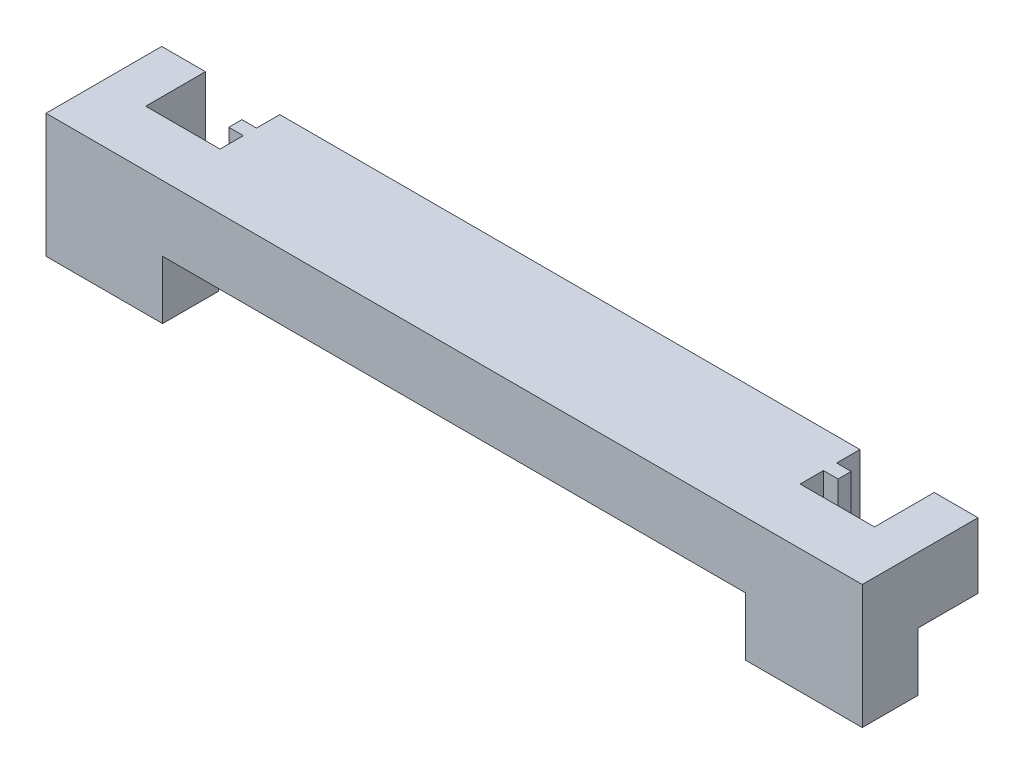
SolidWorks part; units mm, degrees
ref_plane "Ön Düzlem" through (0, 0, 0) normal (0, 0, 1) x (1, 0, 0)
ref_plane "Üst Düzlem" through (0, 0, 0) normal (0, 1, 0) x (1, 0, 0)
ref_plane "Sağ Düzlem" through (0, 0, 0) normal (1, 0, 0) x (0, 0, -1)
sketch "Çizim1" plane through (0, 0, 0) normal (0, 1, 0) x (1, 0, 0)
  line L0 (-14, 1.9354) -> (-14, 3.9854)
  line L5 (-14, 0.0154) -> (14, 0.0154)
  line L6 (-14, 3.9854) -> (-12.5, 3.9854)
  line L11 (-12.5, 3.9854) -> (-12.5, 1.9354)
  line L13 (14, 0.0154) -> (14, 1.9354)
  line L14 (12.5, 1.9354) -> (9.95, 1.9354)
  line L22 (9.95, 1.9354) -> (9.95, 3.9854)
  line L23 (9.95, 3.9854) -> (-9.95, 3.9854)
  line L24 (-9.95, 3.9854) -> (-9.95, 1.9354)
  line L25 (-9.95, 1.9354) -> (-12.5, 1.9354)
  line L26 (-14, 1.9354) -> (-14, 0.0154)
  line L27 (14, 1.9354) -> (14, 3.9854)
  line L28 (14, 3.9854) -> (12.5, 3.9854)
  line L29 (12.5, 3.9854) -> (12.5, 1.9354)
  line L31 (-10.45, 3.1854) -> (-9.45, 3.1854)
  line L32 (-10.45, 3.1854) -> (-10.45, 2.7354)
  line L33 (-10.45, 2.7354) -> (-9.45, 2.7354)
  line L34 (-9.45, 3.1854) -> (-9.45, 2.7354)
  line L35 (-10.45, 3.1854) -> (-9.45, 2.7354) construction
  line L36 (-10.45, 2.7354) -> (-9.45, 3.1854) construction
  line L37 (9.45, 3.1854) -> (10.45, 3.1854)
  line L38 (9.45, 3.1854) -> (9.45, 2.7354)
  line L39 (9.45, 2.7354) -> (10.45, 2.7354)
  line L40 (10.45, 3.1854) -> (10.45, 2.7354)
  line L41 (9.45, 3.1854) -> (10.45, 2.7354) construction
  line L42 (9.45, 2.7354) -> (10.45, 3.1854) construction
  point P4 (0, 3.9854)
  point P15 (-9.95, 2.9604)
  point P21 (9.95, 2.9604)
  dimension "D1" = 19.9
  dimension "D2" = 28
  dimension "D3" = 2.05
  dimension "D4" = 2.55
  dimension "D5" = 3.97
  dimension "D6" = 0.45
  dimension "D7" = 1
  dimension "D8" = 0.45
  dimension "D9" = 1
extrude "Yükseklik-Ekstrüzyon1" add sketch "Çizim1" along normal blind 2.25
sketch "Çizim5" plane through (0, 0, 0) normal (0, -1, 0) x (1, 0, 0)
  line L1 (-14, -0.0154) -> (-10, -0.0154)
  line L2 (-14, -0.0154) -> (-14, -1.9354)
  line L3 (-14, -1.9354) -> (-10, -1.9354)
  line L4 (-10, -0.0154) -> (-10, -1.9354)
  line L5 (10, -1.9354) -> (14, -1.9354)
  line L6 (10, -1.9354) -> (10, -0.0154)
  line L7 (10, -0.0154) -> (14, -0.0154)
  line L8 (14, -1.9354) -> (14, -0.0154)
  point P12 (0, 0)
  dimension "D1" = 20
extrude "Yükseklik-Ekstrüzyon4" add sketch "Çizim5" along normal blind 2
